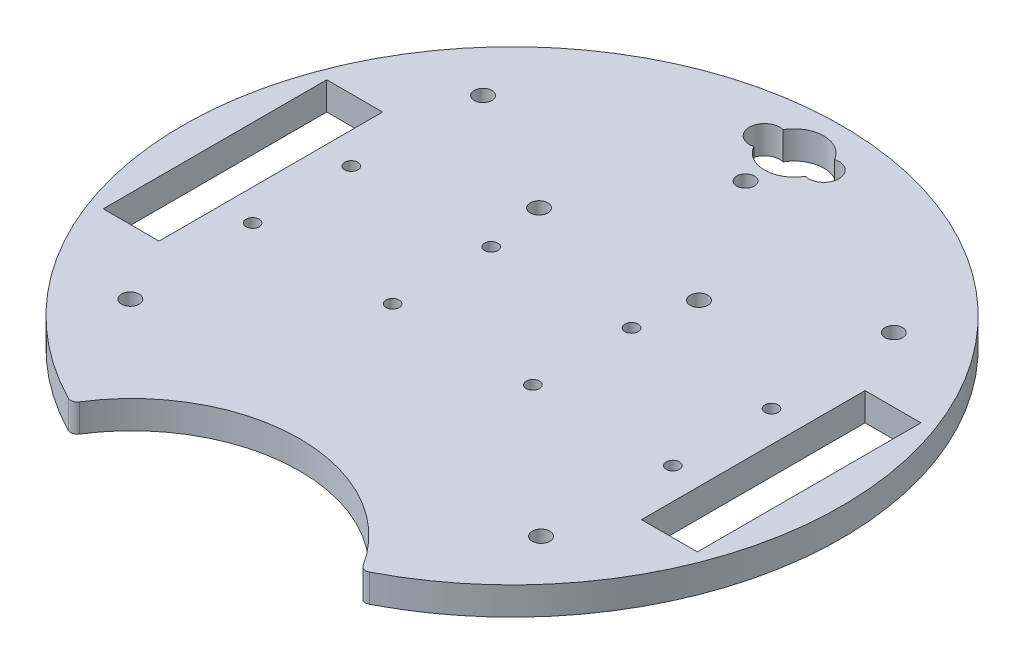
SolidWorks part; units mm, degrees
ref_plane "Front Plane" through (0, 0, 0) normal (0, 0, 1) x (1, 0, 0)
ref_plane "Top Plane" through (0, 0, 0) normal (0, 1, 0) x (1, 0, 0)
ref_plane "Right Plane" through (0, 0, 0) normal (1, 0, 0) x (0, 0, -1)
sketch "Sketch1" plane through (0, 0, 0) normal (0, 1, 0) x (1, 0, 0)
  line L1 (0, 86.2583) -> (0, -96.8543) construction
  line L3 (-32.9956, -67.352) -> (0, -86.402) construction
  line L4 (32.9956, -67.352) -> (0, -86.402) construction
  line L9 (54.8141, -25.4) -> (54.8141, 25.4)
  line L10 (-67.5141, -25.4) -> (-54.8141, -25.4)
  line L11 (-67.5141, -25.4) -> (-67.5141, 25.4)
  line L12 (-67.5141, 25.4) -> (-54.8141, 25.4)
  line L13 (-54.8141, 25.4) -> (-54.8141, -25.4)
  line L14 (67.5141, 25.4) -> (54.8141, 25.4)
  line L15 (67.5141, -25.4) -> (67.5141, 25.4)
  line L16 (67.5141, -25.4) -> (54.8141, -25.4)
  arc A1 (32.2407, -66.1006) -> (-32.2407, -66.1006) centre (0, -86.402) ccw
  arc A2 (34.1948, -66.6358) -> (-34.1948, -66.6358) centre (0, 0) ccw
  arc A3 (5.8576, 67.4236) -> (-5.8539, 67.4301) centre (0, 64.1077) ccw
  arc A4 (-5.8539, 67.4301) -> (-5.8539, 60.7853) centre (-6.731, 64.1077) ccw
  arc A5 (5.8576, 60.7918) -> (5.8576, 67.4236) centre (6.731, 64.1077) ccw
  arc A6 (-5.8539, 60.7853) -> (5.8576, 60.7918) centre (0, 64.1077) ccw
  circle A25 centre (-18.179, 24.3106) radius 2
  circle A38 centre (-46.6637, -40.0812) radius 2
  circle A39 centre (46.6637, -40.0812) radius 2
  circle A40 centre (46.6637, 40.0812) radius 2
  circle A41 centre (-46.6637, 40.0812) radius 2
  arc A42 (-34.1948, -66.6358) -> (-32.2407, -66.1006) centre (-33.51, -65.3013) ccw
  arc A43 (34.1948, -66.6358) -> (32.2407, -66.1006) centre (33.51, -65.3013) cw
  circle A44 centre (-6.731, 64.1077) radius 1.143
  circle A45 centre (6.731, 64.1077) radius 1.143
  circle A47 centre (18.179, 24.3106) radius 2
  circle A48 centre (0, 53.0612) radius 2
  dimension "D3" = 120
  dimension "D15" = 13.462
  dimension "D18" = 2.286
  dimension "D12" = 4
  dimension "D4" = 50.8
  dimension "D5" = 12.7
extrude "Boss-Extrude3" add sketch "Sketch1" along normal blind 6.35 contours A43 A2 A42 A1 A48 A47 A40 A39 A38 L15 L16 L9 L14 L12 L13 L10 L11 A6 A4 A3 A5 A25 A41
sketch "Sketch2" plane through (0, 0, 0) normal (0, 1, 0) x (1, 0, 0)
  line L0 (-74.8974, 0) -> (74.8974, 0) construction
  line L1 (0, 31.1346) -> (0, -55.175) construction
  arc A0 (34.1948, -66.6358) -> (-34.1948, -66.6358) centre (0, 0) ccw construction
  circle A1 centre (-47.7457, 11.205) radius 1.5
  circle A2 centre (-47.7457, -11.205) radius 1.5
  circle A3 centre (-15.9457, 11.205) radius 1.5
  circle A4 centre (-15.9457, -11.205) radius 1.5
  circle A5 centre (15.9457, -11.205) radius 1.5
  circle A6 centre (15.9457, 11.205) radius 1.5
  circle A7 centre (47.7457, -11.205) radius 1.5
  circle A8 centre (47.7457, 11.205) radius 1.5
  dimension "D1" = 3
  dimension "D2" = 3
  dimension "D3" = 31.8
  dimension "D4" = 22.41
extrude "Cut-Extrude2" cut sketch "Sketch2" along normal blind 10
